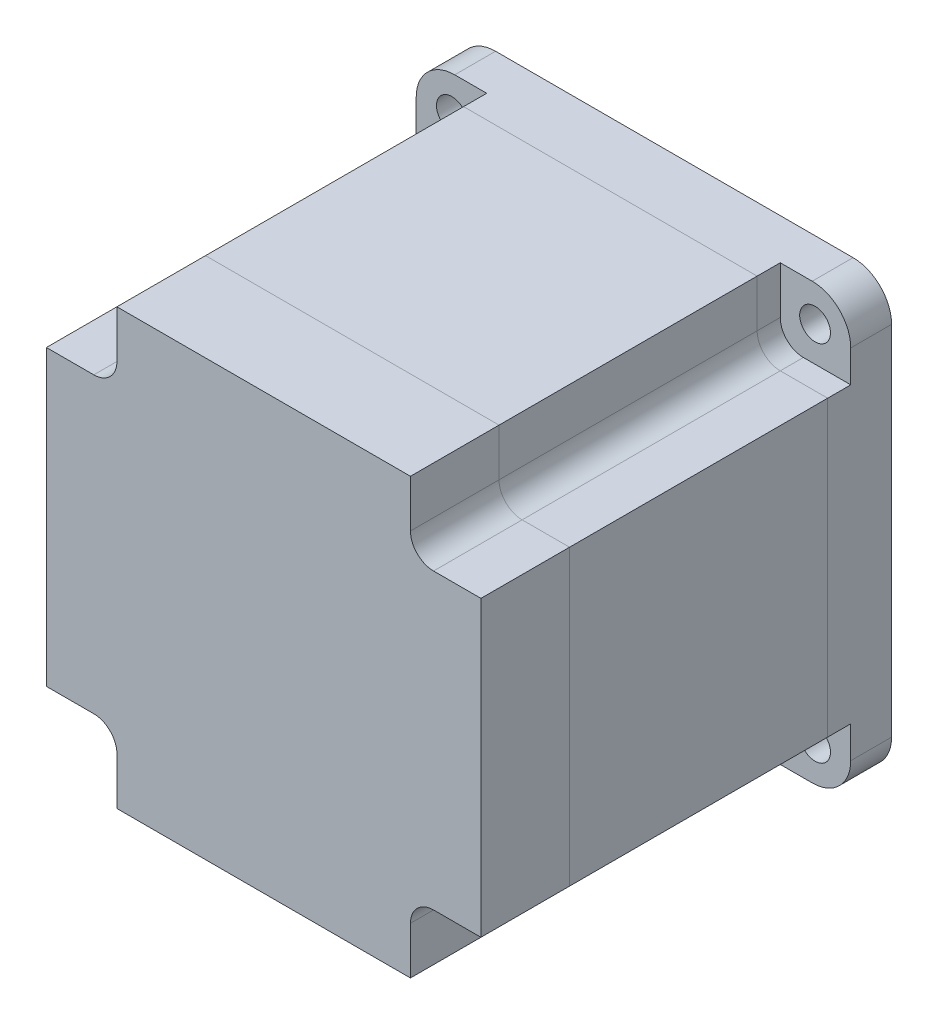
SolidWorks part; units mm, degrees
ref_plane "Alzado" through (0, 0, 0) normal (0, 0, 1) x (1, 0, 0)
ref_plane "Planta" through (0, 0, 0) normal (0, 1, 0) x (1, 0, 0)
ref_plane "Vista lateral" through (0, 0, 0) normal (1, 0, 0) x (0, 0, -1)
sketch "Croquis1" plane through (0, 0, 0) normal (0, 0, 1) x (1, 0, 0)
  line L1 (23.2, -28.2) -> (-23.2, -28.2)
  line L2 (28.2, -23.2) -> (28.2, 23.2)
  line L3 (23.2, 28.2) -> (-23.2, 28.2)
  line L4 (-28.2, -23.2) -> (-28.2, 23.2)
  line L5 (28.2, -28.2) -> (-28.2, 28.2) construction
  line L6 (28.2, 28.2) -> (-28.2, -28.2) construction
  line L7 (-23.57, 23.57) -> (23.57, 23.57) construction
  line L8 (-23.57, 23.57) -> (-23.57, -23.57) construction
  line L9 (-23.57, -23.57) -> (23.57, -23.57) construction
  line L10 (23.57, 23.57) -> (23.57, -23.57) construction
  line L11 (-23.57, 23.57) -> (23.57, -23.57) construction
  line L12 (-23.57, -23.57) -> (23.57, 23.57) construction
  circle A0 centre (-23.57, -23.57) radius 2
  circle A1 centre (23.57, -23.57) radius 2
  circle A2 centre (-23.57, 23.57) radius 2
  circle A3 centre (23.57, 23.57) radius 2
  arc A4 (23.2, -28.2) -> (28.2, -23.2) centre (23.2, -23.2) ccw
  arc A5 (28.2, 23.2) -> (23.2, 28.2) centre (23.2, 23.2) ccw
  arc A6 (-23.2, 28.2) -> (-28.2, 23.2) centre (-23.2, 23.2) ccw
  arc A7 (-28.2, -23.2) -> (-23.2, -28.2) centre (-23.2, -23.2) ccw
  point P0 (0, 0)
  point P6 (0, 0)
  dimension "D5" = 4
  dimension "D6" = 4
  dimension "D7" = 4
  dimension "D8" = 4
  dimension "D9" = 5
  dimension "D10" = 5
  dimension "D1" = 56.4
  dimension "D2" = 56.4
  dimension "D3" = 47.14
  dimension "D4" = 47.14
extrude "Saliente-Extruir1" add sketch "Croquis1" along normal blind 5.3
sketch "Croquis2" plane through (0, 0, 5.3) normal (0, 0, 1) x (1, 0, 0)
  line L0 (-19.05, 22.05) -> (-19.05, 28.2)
  line L1 (23.57, -23.57) -> (-23.57, -23.57) construction
  line L2 (23.57, -23.57) -> (23.57, 23.57) construction
  line L3 (23.57, 23.57) -> (-23.57, 23.57) construction
  line L4 (-23.57, -23.57) -> (-23.57, 23.57) construction
  line L5 (23.57, -23.57) -> (-23.57, 23.57) construction
  line L6 (23.57, 23.57) -> (-23.57, -23.57) construction
  line L11 (-19.05, 19.05) -> (19.05, -19.05) construction
  line L12 (-19.05, -19.05) -> (19.05, 19.05) construction
  line L13 (23.2, 28.2) -> (-23.2, 28.2) construction
  line L14 (-19.05, 28.2) -> (19.05, 28.2)
  line L15 (19.05, 28.2) -> (19.05, 22.05)
  line L16 (-19.05, -22.05) -> (-19.05, -28.2)
  line L17 (-23.2, -28.2) -> (23.2, -28.2) construction
  line L18 (-19.05, -28.2) -> (19.05, -28.2)
  line L19 (19.05, -28.2) -> (19.05, -22.05)
  line L20 (-22.05, 19.05) -> (-28.2, 19.05)
  line L21 (-28.2, 23.2) -> (-28.2, -23.2) construction
  line L22 (-28.2, 19.05) -> (-28.2, -19.05)
  line L23 (-28.2, -19.05) -> (-22.05, -19.05)
  line L24 (22.05, -19.05) -> (28.2, -19.05)
  line L25 (28.2, -23.2) -> (28.2, 23.2) construction
  line L26 (28.2, -19.05) -> (28.2, 19.05)
  line L27 (28.2, 19.05) -> (22.05, 19.05)
  arc A0 (-19.05, -22.05) -> (-22.05, -19.05) centre (-22.05, -22.05) ccw
  arc A1 (22.05, -19.05) -> (19.05, -22.05) centre (22.05, -22.05) ccw
  arc A2 (19.05, 22.05) -> (22.05, 19.05) centre (22.05, 22.05) ccw
  arc A3 (-22.05, 19.05) -> (-19.05, 22.05) centre (-22.05, 22.05) ccw
  point P0 (0, 0)
  point P6 (0, 0)
  dimension "D5" = 3
  dimension "D1" = 47.14
  dimension "D2" = 47.14
  dimension "D3" = 38.1
  dimension "D4" = 38.1
extrude "Saliente-Extruir2" add sketch "Croquis2" along normal blind 3 contours A2 L15 L14 L0 A3 L20 L22 L23 A0 L16 L18 L19 A1 L24 L26 L27
sketch "Croquis3" plane through (0, 0, 8.3) normal (0, 0, 1) x (1, 0, 0)
  line L0 (-19.05, 28.2) -> (19.05, 28.2)
  line L1 (28.2, 19.05) -> (28.2, -19.05)
  line L2 (28.2, -19.05) -> (22.05, -19.05)
  line L3 (-28.2, -19.05) -> (-28.2, 19.05)
  line L4 (-28.2, 19.05) -> (-22.05, 19.05)
  line L5 (-19.05, -28.2) -> (19.05, -28.2)
  line L6 (19.05, -28.2) -> (19.05, -22.05)
  line L7 (-19.05, 28.2) -> (-19.05, 22.05)
  line L8 (22.05, 19.05) -> (28.2, 19.05)
  line L9 (-19.05, -22.05) -> (-19.05, -28.2)
  line L10 (19.05, 22.05) -> (19.05, 28.2)
  line L11 (-22.05, -19.05) -> (-28.2, -19.05)
  arc A0 (-19.05, -22.05) -> (-22.05, -19.05) centre (-22.05, -22.05) ccw
  arc A1 (19.05, -22.05) -> (22.05, -19.05) centre (22.05, -22.05) cw
  arc A2 (22.05, 19.05) -> (19.05, 22.05) centre (22.05, 22.05) cw
  arc A3 (-22.05, 19.05) -> (-19.05, 22.05) centre (-22.05, 22.05) ccw
  point P22 (-19.05, -19.05)
  point P27 (19.05, 19.05)
  dimension "D1" = 3
extrude "Saliente-Extruir4" add sketch "Croquis3" along normal blind 33.5 separate body contours L3 L4 A3 L7 L0 L10 A2 L8 L1 L2 A1 L6 L5 L9 A0 L11
sketch "Croquis5" plane through (0, 0, 41.8) normal (0, 0, 1) x (1, 0, 0)
  line L0 (22.05, 19.05) -> (28.2, 19.05)
  line L1 (-19.05, -28.2) -> (19.05, -28.2)
  line L2 (-19.05, -28.2) -> (-19.05, -22.05)
  line L3 (-19.05, 28.2) -> (19.05, 28.2)
  line L4 (19.05, -28.2) -> (19.05, -22.05)
  line L5 (-19.05, -28.2) -> (19.05, 28.2) construction
  line L6 (-19.05, 28.2) -> (19.05, -28.2) construction
  line L7 (-28.2, 19.05) -> (-22.05, 19.05)
  line L8 (-28.2, 19.05) -> (-28.2, -19.05)
  line L9 (-28.2, -19.05) -> (-22.05, -19.05)
  line L10 (28.2, 19.05) -> (28.2, -19.05)
  line L11 (-28.2, 19.05) -> (28.2, -19.05) construction
  line L12 (-28.2, -19.05) -> (28.2, 19.05) construction
  line L13 (19.05, 22.05) -> (19.05, 28.2)
  line L14 (22.05, -19.05) -> (28.2, -19.05)
  line L15 (-19.05, 22.05) -> (-19.05, 28.2)
  arc A0 (-22.05, -19.05) -> (-19.05, -22.05) centre (-22.05, -22.05) cw
  arc A1 (19.05, -22.05) -> (22.05, -19.05) centre (22.05, -22.05) cw
  arc A2 (22.05, 19.05) -> (19.05, 22.05) centre (22.05, 22.05) cw
  arc A3 (-22.05, 19.05) -> (-19.05, 22.05) centre (-22.05, 22.05) ccw
  point P0 (0, 0)
  point P7 (0, 0)
  point P21 (19.05, -19.05)
  point P24 (19.05, 19.05)
  point P27 (-19.05, 19.05)
  dimension "D1" = 3
extrude "Saliente-Extruir7" add sketch "Croquis5" along normal blind 11.5 separate body contours L1 L4 A1 L14 L10 L0 A2 L13 L3 L15 A3 L7 L8 L9 A0 L2
sketch "Croquis7" plane through (0, 0, 0) normal (0, 0, -1) x (-1, 0, 0)
  circle A0 centre (0, 0) radius 19.05
  circle A1 centre (0, 0) radius 15.25
  circle A2 centre (0, 0) radius 12.55
  circle A3 centre (0, 0) radius 5
extrude "Saliente-Extruir9" add sketch "Croquis7" along normal blind 1.6 separate body contours A0 A1 | A2 A3
sketch "Croquis8" plane through (0, 0, 0) normal (0, 0, -1) x (-1, 0, 0)
  circle A0 centre (0, 0) radius 3.2
extrude "Saliente-Extruir10" add sketch "Croquis8" along normal blind 24
